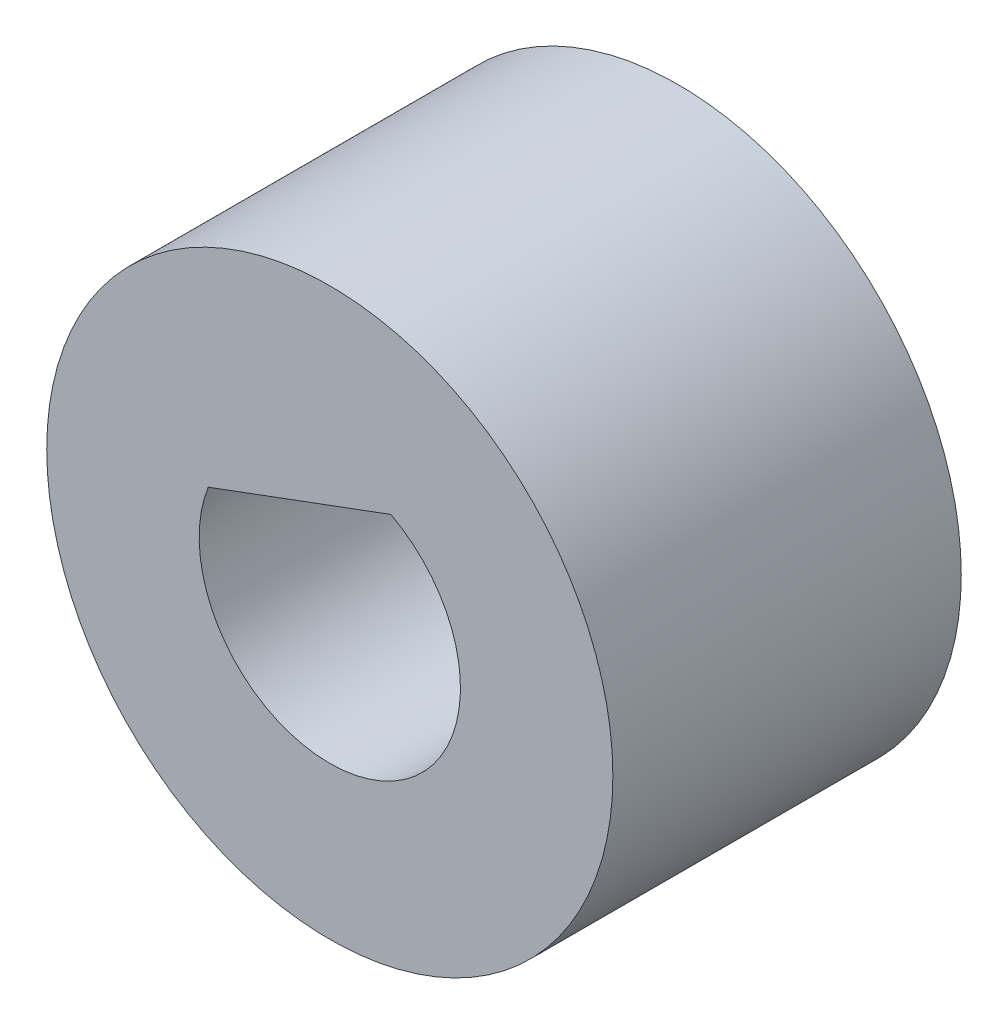
SolidWorks part; units mm, degrees
ref_plane "Front Plane" through (0, 0, 0) normal (0, 0, 1) x (1, 0, 0)
ref_plane "Top Plane" through (0, 0, 0) normal (0, 1, 0) x (1, 0, 0)
ref_plane "Right Plane" through (0, 0, 0) normal (1, 0, 0) x (0, 0, -1)
sketch "Sketch1" plane through (0, 0, 0) normal (0, 0, 1) x (1, 0, 0)
  circle A0 centre (0, 0) radius 1.5
  circle A1 centre (0, 0) radius 3.25
  dimension "D1" = 3
  dimension "D2" = 6.5
extrude "Boss-Extrude1" add sketch "Sketch1" along normal blind 4
sketch "Sketch2" plane through (0, 0, 4) normal (0, 0, 1) x (1, 0, 0)
  line L0 (-1.3959, 0.5492) -> (0.7008, 1.3262)
  line L2 (-1.3959, 0.5492) -> (0.7008, 1.3262) construction
  circle A0 centre (0, 0) radius 1.5
  dimension "D1" = 3
extrude "Boss-Extrude2" add sketch "Sketch2" against normal up to surface (4 mm away) up to face at (3.25, 0, 0)
